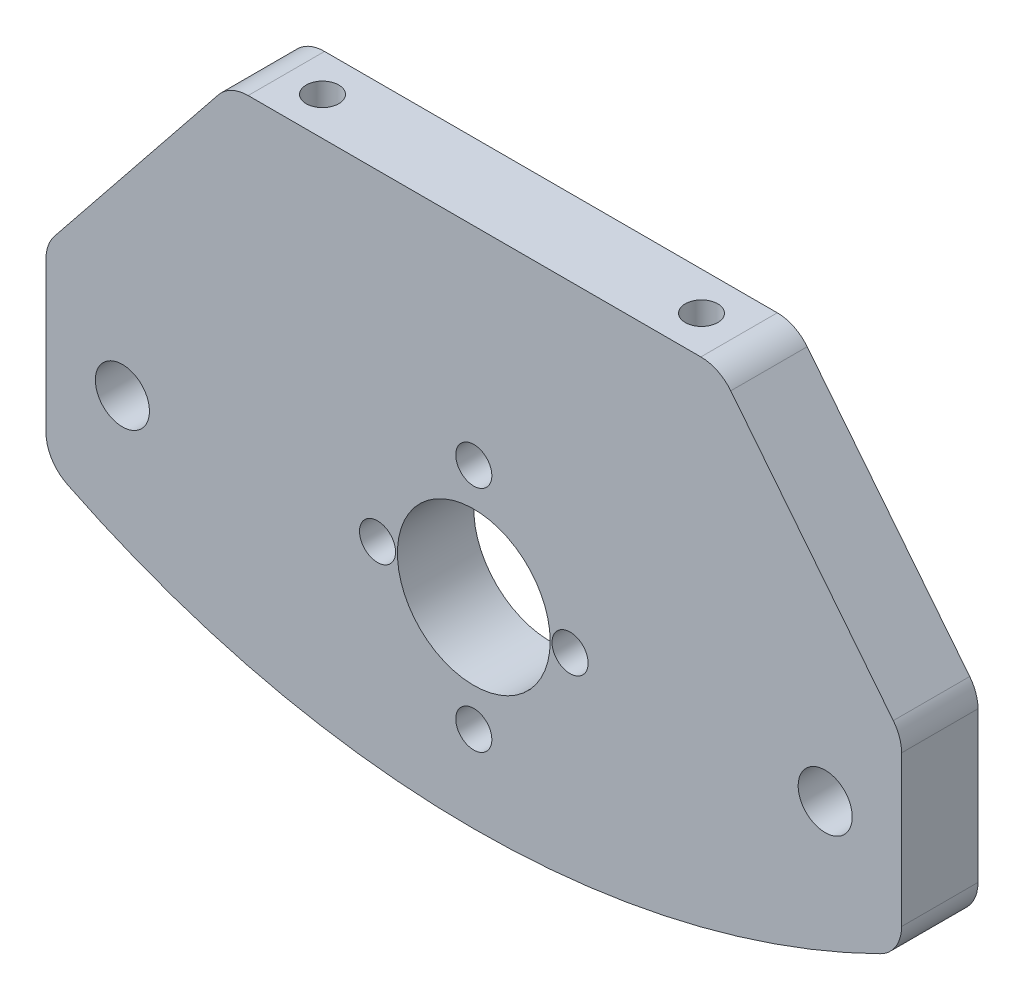
SolidWorks part; units mm, degrees
material "6061-T6 (SS)"
ref_plane "Front Plane" through (0, 0, 0) normal (0, 0, 1) x (1, 0, 0)
ref_plane "Top Plane" through (0, 0, 0) normal (0, 1, 0) x (1, 0, 0)
ref_plane "Right Plane" through (0, 0, 0) normal (1, 0, 0) x (0, 0, -1)
sketch "Sketch1" plane through (0, 0, 0) normal (0, 0, 1) x (1, 0, 0)
  line L0 (-22.1, -23.741) -> (-11.5, -23.741) construction
  line L1 (-35.555, 26.734) -> (35.555, 26.734)
  line L2 (-35.555, 26.734) -> (-35.555, -26.916)
  line L3 (-35.555, -26.916) -> (35.555, -26.916)
  line L4 (35.555, 26.734) -> (35.555, -26.916)
  line L5 (11.5, -23.741) -> (22.1, -23.741) construction
  line L6 (-22.1, -23.741) -> (-11.5, -23.741) construction
  line L7 (11.5, -23.741) -> (22.1, -23.741) construction
  line L8 (-11.5, 23.559) -> (-22.1, 23.559) construction
  line L9 (22.1, 23.559) -> (11.5, 23.559) construction
  line L10 (-11.5, 23.559) -> (-22.1, 23.559) construction
  line L11 (22.1, 23.559) -> (11.5, 23.559) construction
  line L12 (-8, 0) -> (8, 0) construction
  line L13 (0, -9.5) -> (0, 9.5) construction
  circle A0 centre (0, 0) radius 6.35
  circle A2 centre (-8, 0) radius 1.5
  circle A3 centre (0, 9.5) radius 1.5
  circle A4 centre (8, 0) radius 1.5
  circle A5 centre (0, 0) radius 8 construction
  arc A21 (-29.205, -4.8535) -> (-25.0806, -2.4722) centre (-29.205, -0.091) ccw
  arc A22 (-25.0806, -2.4722) -> (-25.0806, 2.2903) centre (-29.205, -0.091) ccw
  arc A23 (-25.0806, 2.2903) -> (-29.205, 4.6715) centre (-29.205, -0.091) ccw
  arc A24 (-29.205, 4.6715) -> (-33.3294, 2.2903) centre (-29.205, -0.091) ccw
  arc A25 (-33.3294, 2.2903) -> (-33.3294, -2.4722) centre (-29.205, -0.091) ccw
  arc A26 (-33.3294, -2.4722) -> (-29.205, -4.8535) centre (-29.205, -0.091) ccw
  arc A27 (-29.205, -4.8535) -> (-25.0806, -2.4722) centre (-29.205, -0.091) ccw construction
  arc A28 (-25.0806, -2.4722) -> (-25.0806, 2.2903) centre (-29.205, -0.091) ccw construction
  arc A29 (-25.0806, 2.2903) -> (-29.205, 4.6715) centre (-29.205, -0.091) ccw construction
  arc A30 (-29.205, 4.6715) -> (-33.3294, 2.2903) centre (-29.205, -0.091) ccw construction
  arc A31 (-33.3294, 2.2903) -> (-33.3294, -2.4722) centre (-29.205, -0.091) ccw construction
  arc A32 (-33.3294, -2.4722) -> (-29.205, -4.8535) centre (-29.205, -0.091) ccw construction
  arc A33 (33.3294, -2.4722) -> (33.3294, 2.2903) centre (29.205, -0.091) ccw
  arc A34 (33.3294, 2.2903) -> (29.205, 4.6715) centre (29.205, -0.091) ccw
  arc A35 (29.205, 4.6715) -> (25.0806, 2.2903) centre (29.205, -0.091) ccw
  arc A36 (25.0806, 2.2903) -> (25.0806, -2.4722) centre (29.205, -0.091) ccw
  arc A37 (25.0806, -2.4722) -> (29.205, -4.8535) centre (29.205, -0.091) ccw
  arc A38 (29.205, -4.8535) -> (33.3294, -2.4722) centre (29.205, -0.091) ccw
  arc A39 (33.3294, -2.4722) -> (33.3294, 2.2903) centre (29.205, -0.091) ccw construction
  arc A40 (33.3294, 2.2903) -> (29.205, 4.6715) centre (29.205, -0.091) ccw construction
  arc A41 (29.205, 4.6715) -> (25.0806, 2.2903) centre (29.205, -0.091) ccw construction
  arc A42 (25.0806, 2.2903) -> (25.0806, -2.4722) centre (29.205, -0.091) ccw construction
  arc A43 (25.0806, -2.4722) -> (29.205, -4.8535) centre (29.205, -0.091) ccw construction
  arc A44 (29.205, -4.8535) -> (33.3294, -2.4722) centre (29.205, -0.091) ccw construction
  circle A13057 centre (0, -9.5) radius 1.5
  point P7 (0, 0)
  dimension "D1" = 12.7
  dimension "D5" = 19
  dimension "D6" = 16
  dimension "D7" = 3
  dimension "D13" = 6.35
  dimension "D14" = 6.35
  dimension "D2" = 3.175
  dimension "D3" = 6.35
  dimension "D15" = 0
  dimension "D16" = 0
extrude "Boss-Extrude1" add sketch "Sketch1" along normal blind 6.35
hole_wizard "#8 Clearance Hole1" positions "Sketch3" profile "Sketch2" hole size "#8" standard "ANSI Inch" end condition through all
sketch "Sketch3" plane through (0, 0, 0) normal (0, 0, -1) x (-1, 0, 0)
  point P0 (-29.205, -0.091)
  point P3 (29.205, -0.091)
sketch "Sketch2" plane through (29.205, -0.091, 0) normal (1, 0, 0) x (0, 1, 0)
  line L0 (0, 0) -> (0, 6.35)
  line L1 (0, 6.35) -> (2.2479, 6.35)
  line L2 (2.2479, 6.35) -> (2.2479, 0)
  line L5 (2.2479, 0) -> (0, 0)
  line L11 (0, -6.35) -> (0, 107.95) construction
  dimension "Thru Hole Dia." = 4.4958
  dimension "Thru Hole Depth" = 6.35
hole_wizard "#6-32 Tapped Hole1" positions "Sketch5" profile "Sketch6" tap size "#6-32" standard "ANSI Inch"
sketch "Sketch5" plane through (0, 26.734, 0) normal (0, 1, 0) x (1, 0, 0)
  point P0 (15.75, -3.175)
  point P3 (-15.75, -3.175)
sketch "Sketch6" plane through (15.75, 26.734, 3.175) normal (1, 0, 0) x (0, 0, 1)
  line L0 (0, 0) -> (0, 26.2127)
  line L1 (0, 26.2127) -> (1.3525, 25.4)
  line L2 (1.3525, 25.4) -> (1.3525, 0)
  line L5 (1.3525, 0) -> (0, 0)
  line L10 (0, 26.2127) -> (-1.3526, 25.4) construction
  line L11 (0, -6.35) -> (0, 107.95) construction
  dimension "Tap Drill Dia." = 2.7051
  dimension "Tap Drill Depth" = 25.4
  dimension "Drill Angle" = 118
cosmetic thread "Hole Thread1" parameters "D1"=17.78, "D2"=3.5052
cosmetic thread "Hole Thread2" parameters "D1"=17.78, "D2"=3.5052
sketch "Sketch7" plane through (0, 0, 0) normal (0, 0, -1) x (-1, 0, 0)
  line L0 (-35.555, 7.684) -> (-20.4045, 26.734)
  line L1 (-35.555, -26.916) -> (-35.555, 26.734) construction
  line L2 (-35.555, 26.734) -> (35.555, 26.734) construction
  line L3 (20.2775, 26.734) -> (35.555, 7.684)
  line L4 (35.555, 26.734) -> (35.555, -26.916) construction
  line L5 (35.555, 7.684) -> (35.555, -7.866) construction
  line L6 (-35.555, 7.684) -> (-35.555, -7.866) construction
  line L7 (-35.555, -0.091) -> (35.555, -0.091) construction
  line L8 (-35.555, -7.866) -> (-35.555, -26.916)
  line L9 (-35.555, -26.916) -> (35.555, -26.916)
  line L10 (35.555, -26.916) -> (35.555, -7.866)
  line L11 (35.555, 7.684) -> (35.555, 26.734)
  line L12 (35.555, 26.734) -> (20.2775, 26.734)
  line L13 (-20.4045, 26.734) -> (-35.555, 26.734)
  line L14 (-35.555, 26.734) -> (-35.555, 7.684)
  arc A0 (-35.555, -7.866) -> (35.555, -7.866) centre (0, 59.5305) ccw
  line M8 (35.555, -26.916) -> (35.555, 26.734)
  line M9 (35.555, 26.734) -> (-35.555, 26.734)
  line M10 (-35.555, 26.734) -> (-35.555, -26.916)
  dimension "D5" = 76.2
  dimension "D1" = 3.175
  dimension "D2" = 3.302
  dimension "D3" = 19.05
extrude "Cut-Extrude1" cut sketch "Sketch7" against normal through all contours L0 M10 M9 | L3 M9 M8 | L9 L10 A0 L8
fillet "Fillet1" radius 3.175 6 edges at (-20.2776, 26.734, 3.175) (20.4046, 26.734, 3.175) (35.555, 7.684, 3.175) (35.555, -7.866, 3.175) (-35.555, 7.684, 3.175) (-35.555, -7.866, 3.175)
